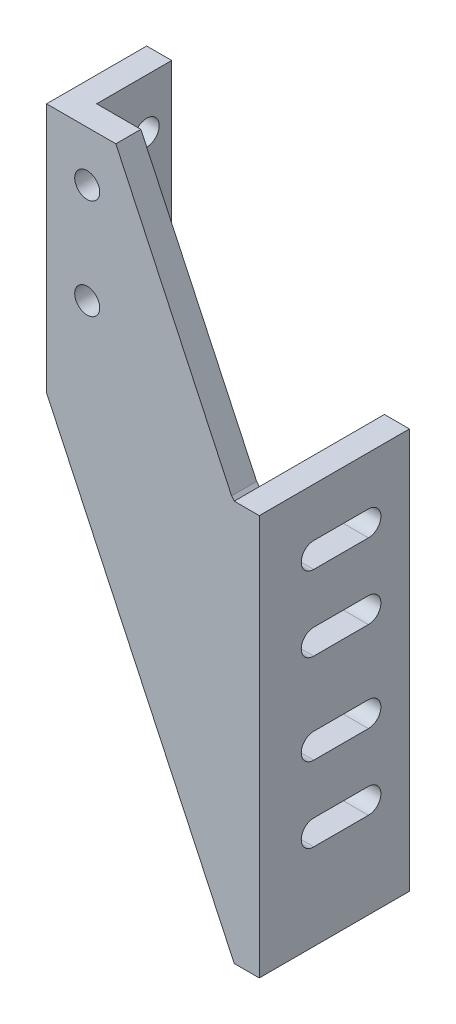
SolidWorks part; units mm, degrees
material "AISI 1018 Steel, Cold Rolled"
ref_plane "Front" through (0, 0, 0) normal (0, 0, 1) x (1, 0, 0)
ref_plane "Top" through (0, 0, 0) normal (0, 1, 0) x (1, 0, 0)
ref_plane "Right" through (0, 0, 0) normal (1, 0, 0) x (0, 0, -1)
sketch "Sketch1" plane through (0, 0, 0) normal (0, 0, 1) x (1, 0, 0)
  line L0 (1.3446, -204.8604) -> (1.3446, -1.6604)
  line L1 (-12.7, 0) -> (-71.4438, 125.3476)
  line L2 (-71.4438, 125.3476) -> (-106.5883, 125.3476)
  line L3 (-106.5883, 125.3476) -> (-106.5883, -1.6524)
  line L4 (-11.3554, -204.8604) -> (1.3446, -204.8604)
  line L5 (1.3446, -1.6604) -> (-11.3554, -1.6604)
  line L6 (-11.3554, -1.6604) -> (-12.7, 0)
  line L8 (-106.5883, -1.6524) -> (-11.3554, -204.8604)
extrude "Extrude1" add sketch "Sketch1" along normal blind 12.7
sketch "Sketch2" plane through (0, 0, 0) normal (0, 0, 1) x (1, 0, 0)
  line L1 (-106.5883, 125.3476) -> (-93.8883, 125.3476)
  line L2 (-106.5883, 125.3476) -> (-106.5883, -1.6524)
  line L3 (-106.5883, -1.6524) -> (-93.8883, -1.6524)
  line L4 (-93.8883, 125.3476) -> (-93.8883, -1.6524)
  dimension "D1" = 127
  dimension "D2" = 12.7
extrude "Extrude2" add sketch "Sketch2" against normal blind 38.1
sketch "Sketch3" plane through (0, 0, 0) normal (0, 0, 1) x (1, 0, 0)
  line L1 (1.3446, -204.8604) -> (-11.3554, -204.8604)
  line L2 (1.3446, -204.8604) -> (1.3446, -1.6604)
  line L3 (1.3446, -1.6604) -> (-11.3554, -1.6604)
  line L4 (-11.3554, -204.8604) -> (-11.3554, -1.6604)
extrude "Extrude3" add sketch "Sketch3" against normal blind 63.5
hole_wizard "1/2-20 Tapped Hole1" positions "3DSketch1" profile "Sketch4" tap size "1/2-20" standard "Ansi Inch" end condition through all
sketch3d "3DSketch1"
  line L0 (-106.5883, 125.3476, -38.1) -> (-106.5883, 125.3476, 12.7) construction
  line L4 (-106.5883, 125.3476, 12.7) -> (-106.5883, -1.6524, 12.7) construction
  point P0 (-106.5883, 99.9476, -25.4)
  dimension "D1" = 25.4
  dimension "D2" = 38.1
sketch "Sketch4" plane through (-106.5883, 99.9476, -25.4) normal (0, 1, 0) x (0, 0, 1)
  line L0 (0, 0) -> (0, 107.9329)
  line L1 (0, 107.9329) -> (6.35, 107.9329)
  line L2 (6.35, 107.9329) -> (6.35, 0)
  line L5 (6.35, 0) -> (0, 0)
  line L11 (0, -6.35) -> (0, 107.95) construction
  dimension "Thread Major Dia." = 12.7
  dimension "Thru Tap Drill Depth" = 107.9329
hole_wizard "1/2-20 Tapped Hole2" positions "3DSketch2" profile "Sketch5" tap size "1/2-20" standard "Ansi Inch" end condition through all
sketch3d "3DSketch2"
  line L0 (-71.4438, 125.3476, 0) -> (-93.8883, 125.3476, 0) construction
  line L1 (-106.5883, 125.3476, 0) -> (-106.5883, -1.6524, 0) construction
  point P0 (-85.9635, 99.9476, 0)
  point P1 (-85.9635, 49.1476, 0)
  dimension "D1" = 25.4
  dimension "D2" = 20.6248
  dimension "D3" = 20.6248
  dimension "D4" = 50.8
sketch "Sketch5" plane through (-85.9635, 99.9476, 0) normal (1, 0, 0) x (0, 1, 0)
  line L0 (0, 0) -> (0, 12.7)
  line L1 (0, 12.7) -> (6.35, 12.7)
  line L2 (6.35, 12.7) -> (6.35, 0)
  line L5 (6.35, 0) -> (0, 0)
  line L11 (0, -6.35) -> (0, 107.95) construction
  dimension "Thread Major Dia." = 12.7
  dimension "Thru Tap Drill Depth" = 12.7
sketch "Sketch6" plane through (1.3446, 0, 0) normal (1, 0, 0) x (0, 0, -1)
  line L1 (14.9451, -26.4254) -> (42.672, -26.4254)
  line L2 (63.5, -1.6604) -> (-12.7, -1.6604) construction
  line L3 (42.672, -39.1254) -> (14.9451, -39.1254)
  line L4 (14.9451, -64.5254) -> (42.672, -64.5254)
  line L5 (14.9451, -110.2454) -> (42.672, -110.2454)
  line L6 (42.672, -77.2254) -> (14.9451, -77.2254)
  line L7 (42.672, -122.9454) -> (14.9451, -122.9454)
  line L8 (14.9451, -148.3454) -> (42.672, -148.3454)
  line L9 (42.672, -161.0454) -> (14.9451, -161.0454)
  line L10 (14.9451, -32.7754) -> (14.9451, -70.8754) construction
  line L11 (14.9451, -70.8754) -> (14.9451, -116.5954) construction
  line L12 (14.9451, -116.5954) -> (14.9451, -154.6954) construction
  line L13 (42.672, -154.6954) -> (42.672, -116.5954) construction
  line L14 (42.672, -116.5954) -> (42.672, -70.8754) construction
  line L15 (42.672, -70.8754) -> (42.672, -32.7754) construction
  line L16 (14.9451, -32.7754) -> (42.672, -32.7754) construction
  line L17 (14.9451, -70.8754) -> (42.672, -70.8754) construction
  line L18 (14.9451, -116.5954) -> (42.672, -116.5954) construction
  line L19 (14.9451, -154.6954) -> (42.672, -154.6954) construction
  line L20 (-12.7, -204.8604) -> (-12.7, -1.6604) construction
  arc A0 (14.9451, -64.5254) -> (14.9451, -77.2254) centre (14.9451, -70.8754) ccw
  arc A1 (42.672, -77.2254) -> (42.672, -64.5254) centre (42.672, -70.8754) ccw
  arc A2 (14.9451, -26.4254) -> (14.9451, -39.1254) centre (14.9451, -32.7754) ccw
  arc A3 (42.672, -39.1254) -> (42.672, -26.4254) centre (42.672, -32.7754) ccw
  arc A4 (14.9451, -148.3454) -> (14.9451, -161.0454) centre (14.9451, -154.6954) ccw
  arc A5 (42.672, -161.0454) -> (42.672, -148.3454) centre (42.672, -154.6954) ccw
  arc A6 (14.9451, -110.2454) -> (14.9451, -122.9454) centre (14.9451, -116.5954) ccw
  arc A7 (42.672, -122.9454) -> (42.672, -110.2454) centre (42.672, -116.5954) ccw
  dimension "D1" = 55.372
  dimension "D2" = 69.215
  dimension "D5" = 6.35
  dimension "D9" = 6.35
  dimension "D3" = 27.7269
  dimension "D6" = 38.1
  dimension "D7" = 45.72
  dimension "D8" = 2
  dimension "D4" = 2
extrude "Cut-Extrude1" cut sketch "Sketch6" against normal up to next
